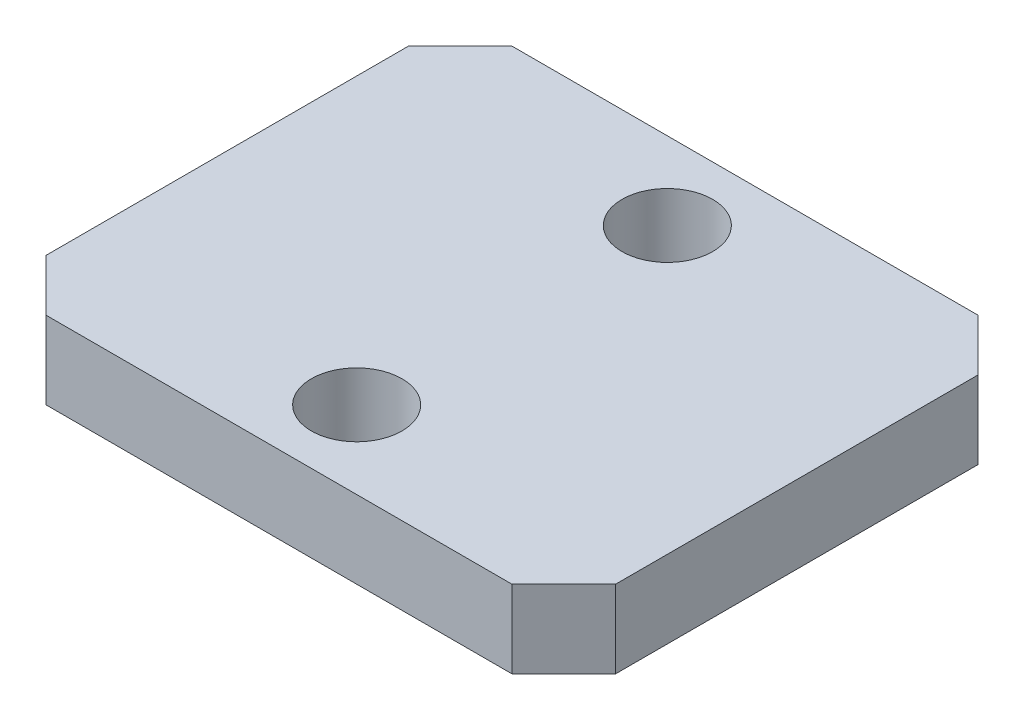
SolidWorks part; units mm, degrees
ref_plane "Front Plane" through (0, 0, 0) normal (0, 0, 1) x (1, 0, 0)
ref_plane "Top Plane" through (0, 0, 0) normal (0, 1, 0) x (1, 0, 0)
ref_plane "Right Plane" through (0, 0, 0) normal (1, 0, 0) x (0, 0, -1)
sketch "Sketch1" plane through (0, 0, 0) normal (0, 1, 0) x (1, 0, 0)
  line L1 (-11, -9) -> (11, -9)
  line L2 (-11, -9) -> (-11, 9)
  line L3 (-11, 9) -> (11, 9)
  line L4 (11, -9) -> (11, 9)
  line L5 (-11, -9) -> (11, 9) construction
  line L6 (-11, 9) -> (11, -9) construction
  point P0 (0, 0)
  dimension "D1" = 22
  dimension "D2" = 18
extrude "Boss-Extrude1" add sketch "Sketch1" along normal blind 3
sketch "Sketch2" plane through (0, 3, 0) normal (0, 1, 0) x (1, 0, 0)
  line L0 (0, 9) -> (0, -9) construction
  line L1 (11, 9) -> (-11, 9) construction
  line L2 (-11, -9) -> (11, -9) construction
  line L3 (-11, 0) -> (11, 0) construction
  line L4 (-11, 9) -> (-11, -9) construction
  line L5 (11, -9) -> (11, 9) construction
  circle A0 centre (0, 6) radius 1.75
  circle A1 centre (0, -6) radius 1.75
  dimension "D1" = 6
  dimension "D2" = 3.5
extrude "Cut-Extrude1" cut sketch "Sketch2" against normal up to next and the other way through all
chamfer "Chamfer1" distance 2 angle 45 4 edges at (11, 1.5, 9) (11, 1.5, -9) (-11, 1.5, -9) (-11, 1.5, 9)
